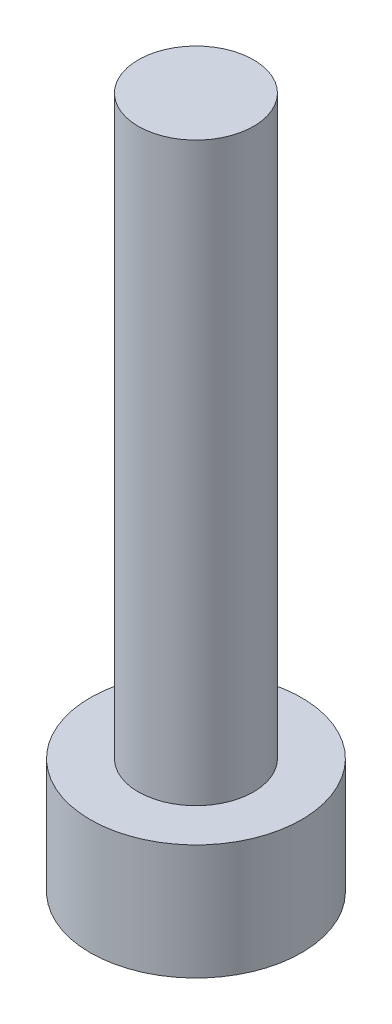
SolidWorks part; units mm, degrees
ref_plane "Front Plane" through (0, 0, 0) normal (0, 0, 1) x (1, 0, 0)
ref_plane "Top Plane" through (0, 0, 0) normal (0, 1, 0) x (1, 0, 0)
ref_plane "Right Plane" through (0, 0, 0) normal (1, 0, 0) x (0, 0, -1)
sketch "Sketch1" plane through (0, 0, 0) normal (0, 1, 0) x (1, 0, 0)
  circle A0 centre (0, 0) radius 2.75
  dimension "D1" = 5.5
extrude "Boss-Extrude1" add sketch "Sketch1" along normal blind 3
sketch "Sketch2" plane through (0, 3, 0) normal (0, 1, 0) x (1, 0, 0)
  circle A0 centre (0, 0) radius 1.5
  point P3 (0, 0)
  dimension "D1" = 3
extrude "Boss-Extrude2" add sketch "Sketch2" along normal blind 15
sketch "Sketch3" plane through (0, 0, 0) normal (0, -1, 0) x (-1, 0, 0)
  line L1 (0, -1.4434) -> (1.25, -0.7217)
  line L2 (1.25, -0.7217) -> (1.25, 0.7217)
  line L3 (1.25, 0.7217) -> (0, 1.4434)
  line L4 (0, 1.4434) -> (-1.25, 0.7217)
  line L5 (-1.25, 0.7217) -> (-1.25, -0.7217)
  line L6 (-1.25, -0.7217) -> (0, -1.4434)
  circle A0 centre (0, 0) radius 1.25 construction
  dimension "D1" = 2.5
extrude "Cut-Extrude1" cut sketch "Sketch3" against normal blind 1.5
